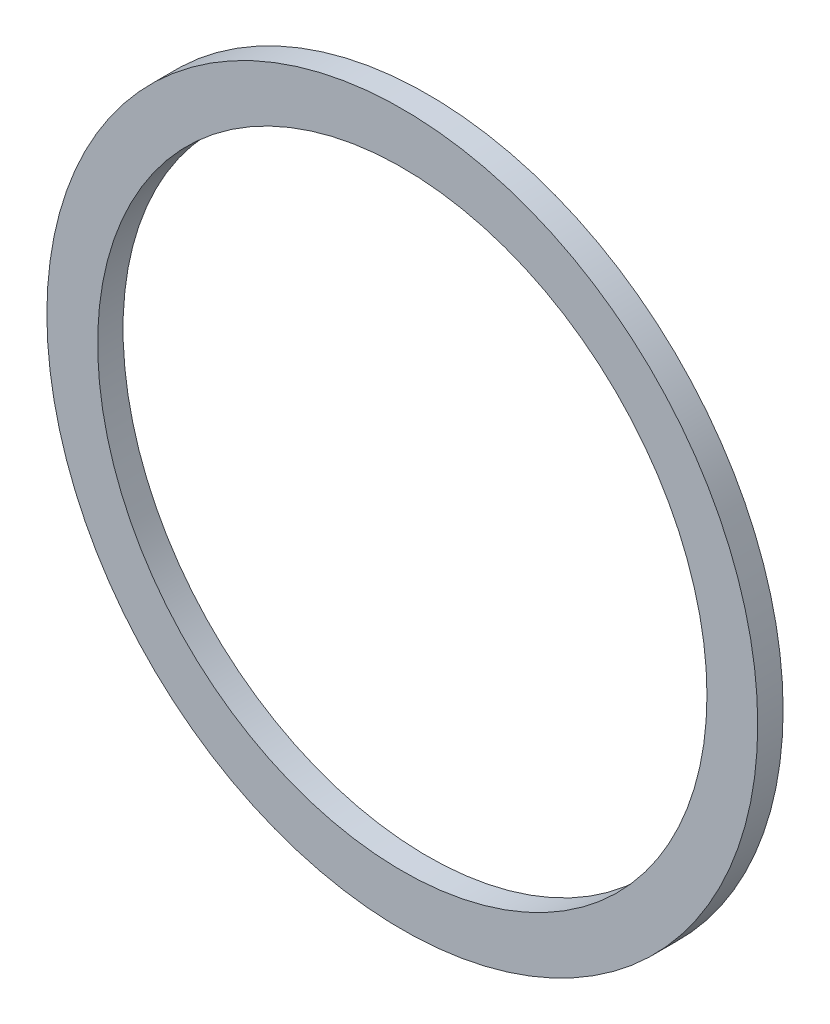
SolidWorks part; units mm, degrees
ref_plane "Plan de face" through (0, 0, 0) normal (0, 0, 1) x (1, 0, 0)
ref_plane "Plan de dessus" through (0, 0, 0) normal (0, 1, 0) x (1, 0, 0)
ref_plane "Plan de droite" through (0, 0, 0) normal (1, 0, 0) x (0, 0, -1)
sketch "Esquisse1" plane through (0, 0, 0) normal (0, 0, 1) x (1, 0, 0)
  circle A0 centre (-0.1, 0.3998) radius 35
  circle A1 centre (-0.1, 0.3998) radius 30
extrude "Boss.-Extru.1" add sketch "Esquisse1" along normal blind 2.5
